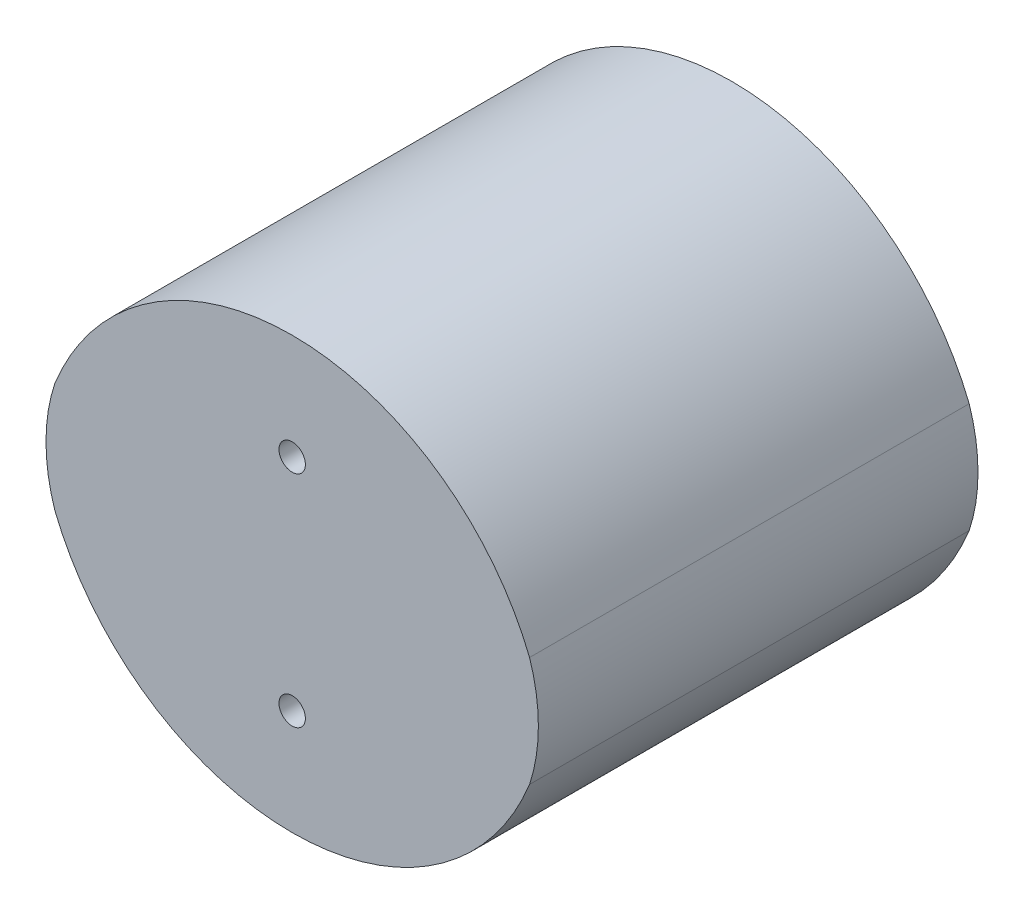
SolidWorks part; units mm, degrees
ref_plane "Plan de face" through (0, 0, 0) normal (0, 0, 1) x (1, 0, 0)
ref_plane "Plan de dessus" through (0, 0, 0) normal (0, 1, 0) x (1, 0, 0)
ref_plane "Plan de droite" through (0, 0, 0) normal (1, 0, 0) x (0, 0, -1)
sketch "Esquisse1" plane through (0, 0, 0) normal (0, 0, 1) x (1, 0, 0)
  line L0 (0, -26.95) -> (0, 26.95) construction
  line L1 (27.5, 0) -> (-27.5, 0) construction
  line L2 (0, -6.25) -> (0, 6.25) construction
  line L3 (-26.9984, 6.25) -> (0, -6.25) construction
  line L4 (26.9984, 6.25) -> (0, -6.25) construction
  line L5 (-26.9984, -6.25) -> (0, 6.25) construction
  line L6 (26.9984, -6.25) -> (0, 6.25) construction
  arc A1 (-26.9984, 6.25) -> (-26.9984, -6.25) centre (-8, 0) ccw
  arc A2 (26.9984, 6.25) -> (26.9984, -6.25) centre (8, 0) cw
  arc A7 (-26.9984, 6.25) -> (26.9984, 6.25) centre (0, -4.5952) cw
  arc A8 (-26.9984, -6.25) -> (26.9984, -6.25) centre (0, 4.5952) ccw
  point P2 (0, 0)
  point P3 (0, -24.5)
  point P4 (28, 0)
  point P5 (0, 24.5)
  point P6 (-28, 0)
  point P22 (28, 0)
extrude "Boss.-Extru.1" add sketch "Esquisse1" along normal blind 50
hole_wizard "Diamètre du perçage Ø3.0 (3)1" positions "Esquisse2" profile "Esquisse3" hole size "Ø3.0" standard "ISO" end condition through all
sketch "Esquisse2" plane through (0, 0, 50) normal (0, 0, 1) x (1, 0, 0)
  point P0 (0, 12.5)
  point P2 (0, -12.5)
sketch "Esquisse3" plane through (0, 12.5, 50) normal (1, 0, 0) x (0, -1, 0)
  line L0 (0, 0) -> (0, 50)
  line L1 (0, 50) -> (1.5, 50)
  line L2 (1.5, 50) -> (1.5, 0)
  line L5 (1.5, 0) -> (0, 0)
  line L11 (0, -6.35) -> (0, 107.95) construction
  dimension "Diamètre du perçage jusqu'au prochain" = 3
  dimension "Profondeur du perçage jusqu'au prochain" = 50
equation "\"D3@Esquisse1\"=\"D2@Esquisse1\"/2"
equation "\"D5@Esquisse1\"=\"D4@Esquisse1\"/2"
equation "\"D2@Esquisse2\"=\"D1@Esquisse2\""
